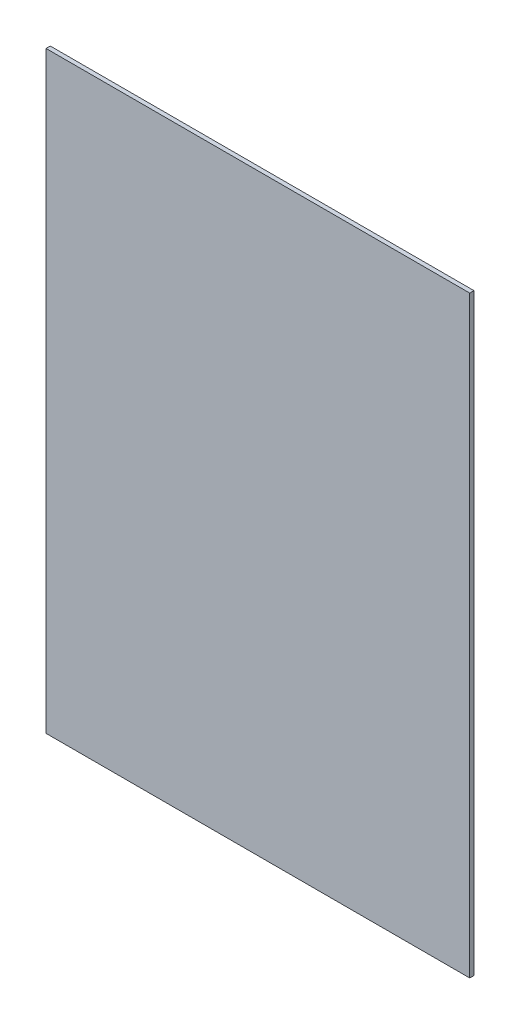
SolidWorks part; units mm, degrees
ref_plane "Alzado" through (0, 0, 0) normal (0, 0, 1) x (1, 0, 0)
ref_plane "Planta" through (0, 0, 0) normal (0, 1, 0) x (1, 0, 0)
ref_plane "Vista lateral" through (0, 0, 0) normal (1, 0, 0) x (0, 0, -1)
sketch "Croquis1" plane through (0, 0, 0) normal (0, 0, 1) x (1, 0, 0)
  line L1 (537.9899, 735.9025) -> (37.9899, 735.9025)
  line L2 (537.9899, 735.9025) -> (537.9899, 35.9025)
  line L3 (537.9899, 35.9025) -> (37.9899, 35.9025)
  line L4 (37.9899, 735.9025) -> (37.9899, 35.9025)
extrude "Saliente-Extruir1" add sketch "Croquis1" along normal blind 5
